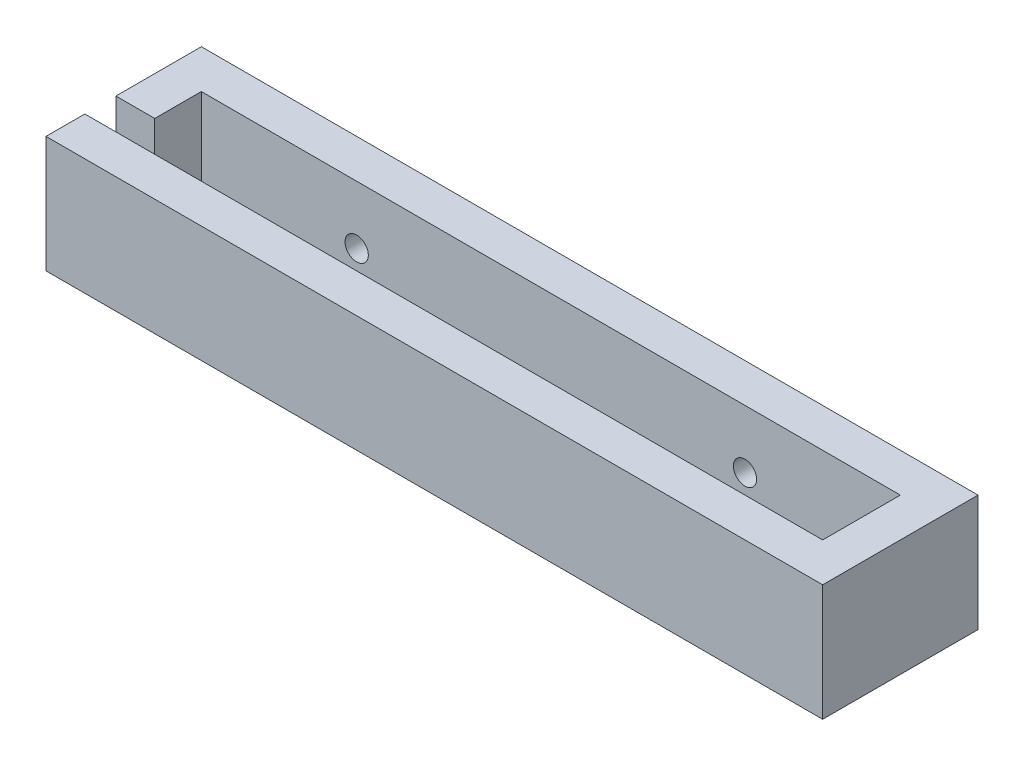
SolidWorks part; units mm, degrees
material "ABS"
ref_plane "前视基准面" through (0, 0, 0) normal (0, 0, 1) x (1, 0, 0)
ref_plane "上视基准面" through (0, 0, 0) normal (0, 1, 0) x (1, 0, 0)
ref_plane "右视基准面" through (0, 0, 0) normal (1, 0, 0) x (0, 0, -1)
sketch "草图2" plane through (0, 0, 0) normal (0, 1, 0) x (1, 0, 0)
  line L1 (-23.2793, 5.6802) -> (76.7207, 5.6802)
  line L2 (-23.2793, 5.6802) -> (-23.2793, -14.3198)
  line L3 (-23.2793, -14.3198) -> (76.7207, -14.3198)
  line L4 (76.7207, 5.6802) -> (76.7207, -14.3198)
  dimension "D1" = 20
  dimension "D2" = 100
extrude "凸台-拉伸1" add sketch "草图2" along normal blind 15
sketch "草图3" plane through (0, 15, 0) normal (0, 1, 0) x (1, 0, 0)
  line L1 (-18.2793, 0.6802) -> (71.7207, 0.6802)
  line L2 (-18.2793, 0.6802) -> (-18.2793, -9.3198)
  line L3 (-18.2793, -9.3198) -> (71.7207, -9.3198)
  line L4 (71.7207, 0.6802) -> (71.7207, -9.3198)
  line L5 (-23.2793, 5.6802) -> (-23.2793, -14.3198) construction
  line L6 (76.7207, 5.6802) -> (-23.2793, 5.6802) construction
  dimension "D1" = 90
  dimension "D2" = 10
  dimension "D3" = 5
  dimension "D4" = 5
extrude "切除-拉伸1" cut sketch "草图3" against normal blind 10
sketch "草图5" plane through (0, 15, 0) normal (0, 1, 0) x (1, 0, 0)
  line L0 (-23.2793, 5.6802) -> (-23.2793, -14.3198) construction
  line L1 (-18.2793, -9.3198) -> (-23.2793, -9.3198)
  line L2 (-18.2793, -9.3198) -> (-18.2793, -5.3198)
  line L3 (-18.2793, -5.3198) -> (-23.2793, -5.3198)
  line L4 (-23.2793, -9.3198) -> (-23.2793, -5.3198)
  dimension "D1" = 4
extrude "切除-拉伸2" cut sketch "草图5" against normal blind 10
sketch "草图6" plane through (0, 0, -5.6802) normal (0, 0, -1) x (-1, 0, 0)
  line L1 (23.2793, 15) -> (23.2793, 0) construction
  line L2 (-76.7207, 15) -> (-76.7207, 0) construction
  line L3 (-76.7207, 0) -> (23.2793, 0) construction
  circle A0 centre (-1.7207, 7.5) radius 1.5
  circle A1 centre (-51.7207, 7.5) radius 1.5
  dimension "D6" = 3
  dimension "D7" = 3
  dimension "D1" = 50
  dimension "D2" = 25
  dimension "D3" = 25
  dimension "D4" = 7.5
  dimension "D5" = 7.5
extrude "切除-拉伸3" cut sketch "草图6" against normal up to next
